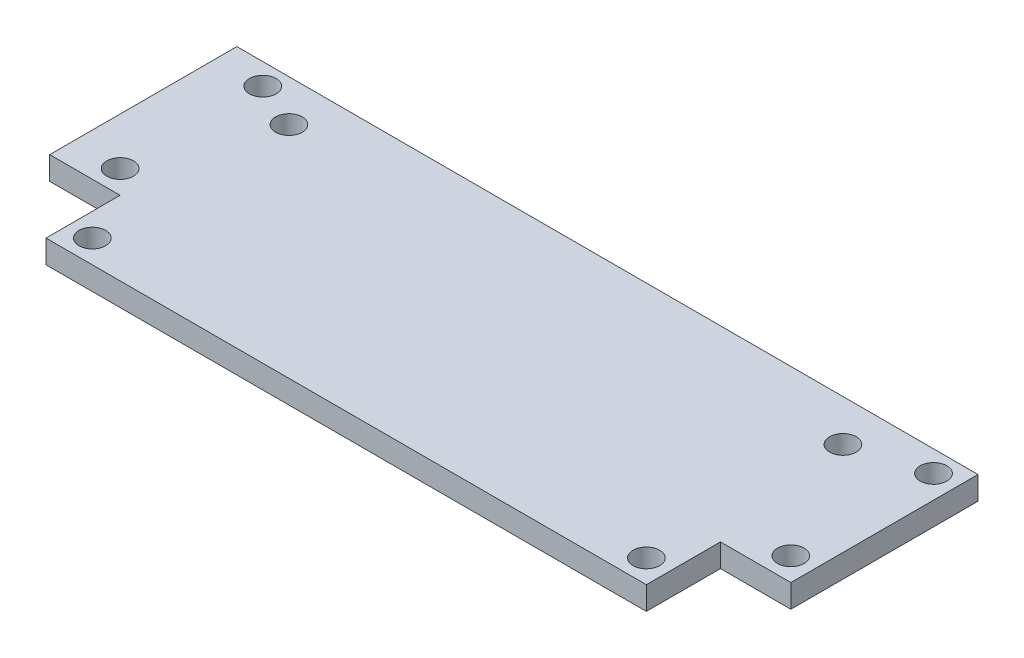
SolidWorks part; units mm, degrees
ref_plane "Front" through (0, 0, 0) normal (0, 0, 1) x (1, 0, 0)
ref_plane "Top" through (0, 0, 0) normal (0, 1, 0) x (1, 0, 0)
ref_plane "Right" through (0, 0, 0) normal (1, 0, 0) x (0, 0, -1)
sketch "Sketch2" plane through (0, 0, 0) normal (0, 1, 0) x (1, 0, 0)
  line L1 (50.8, -17.907) -> (-50.8, -17.907)
  line L2 (50.8, -17.907) -> (50.8, 17.907)
  line L3 (50.8, 17.907) -> (-50.8, 17.907)
  line L4 (-50.8, -17.907) -> (-50.8, 17.907)
  line L5 (50.8, -17.907) -> (-50.8, 17.907) construction
  line L6 (50.8, 17.907) -> (-50.8, -17.907) construction
  point P0 (0, 0)
  dimension "D1" = 101.6
  dimension "D2" = 35.814
extrude "Boss-Extrude1" add sketch "Sketch2" along normal blind 3.175
sketch "Sketch3" plane through (0, 3.175, 0) normal (0, 1, 0) x (1, 0, 0)
  line L0 (50.8, 17.907) -> (47.625, 17.907) construction
  line L1 (50.8, 17.907) -> (-50.8, 17.907) construction
  line L2 (47.625, 17.907) -> (47.625, 14.986) construction
  line L3 (47.625, 14.986) -> (47.625, -4.572) construction
  line L4 (-50.8, 17.907) -> (-47.498, 17.907) construction
  line L5 (-47.498, 17.907) -> (-47.498, -17.907) construction
  line L6 (-50.8, -17.907) -> (50.8, -17.907) construction
  line L7 (-47.498, 17.907) -> (-44.323, 17.907) construction
  line L8 (-44.323, 17.907) -> (-44.323, 14.986) construction
  line L9 (-44.323, 14.986) -> (-44.323, -4.572) construction
  circle A0 centre (47.625, 14.986) radius 1.8288
  circle A1 centre (47.625, -4.572) radius 1.8288
  circle A2 centre (-44.323, 14.986) radius 1.8288
  circle A3 centre (-44.323, -4.572) radius 1.8288
  dimension "D3" = 3.6576
  dimension "D5" = 3.6576
  dimension "D9" = 3.6576
  dimension "D10" = 3.6576
  dimension "D1" = 3.175
  dimension "D2" = 2.921
  dimension "D4" = 19.558
  dimension "D6" = 3.302
  dimension "D7" = 3.175
  dimension "D8" = 2.921
extrude "Cut-Extrude1" cut sketch "Sketch3" against normal through all
sketch "Sketch4" plane through (0, 3.175, 0) normal (0, 1, 0) x (1, 0, 0)
  line L0 (0, 17.907) -> (0, -17.907) construction
  line L1 (50.8, 17.907) -> (-50.8, 17.907) construction
  line L2 (-50.8, -17.907) -> (50.8, -17.907) construction
  line L3 (-44.323, 14.986) -> (-37.973, 14.986) construction
  line L4 (-37.973, -17.907) -> (-37.973, -14.732) construction
  line L5 (-37.973, -14.732) -> (-37.973, 12.2174) construction
  circle A0 centre (-37.973, -14.732) radius 1.8288
  circle A1 centre (-37.973, 12.2174) radius 1.8288
  circle A2 centre (37.973, -14.732) radius 1.8288
  circle A3 centre (37.973, 12.2174) radius 1.8288
  dimension "D2" = 3.175
  dimension "D4" = 26.9494
  dimension "D3" = 3.6576
  dimension "D1" = 6.35
extrude "Cut-Extrude2" cut sketch "Sketch4" against normal through all
sketch "Sketch5" plane through (0, 3.175, 0) normal (0, 1, 0) x (1, 0, 0)
  line L0 (37.973, -14.732) -> (41.148, -14.732) construction
  line L1 (47.625, -4.572) -> (47.625, -7.747) construction
  line L2 (50.8, -17.907) -> (50.8, -7.747)
  line L3 (50.8, -17.907) -> (41.1484, -17.907)
  line L4 (50.8, -7.747) -> (41.1484, -7.747)
  line L5 (41.1484, -17.907) -> (41.1484, -7.747)
  line L6 (50.8, -17.907) -> (50.8, 17.907) construction
  line L7 (0, -17.907) -> (0, 17.907) construction
  line L8 (-50.8, -17.907) -> (50.8, -17.907) construction
  line L9 (50.8, 17.907) -> (-50.8, 17.907) construction
  line L10 (-50.8, -17.907) -> (-50.8, -7.747)
  line L11 (-50.8, -17.907) -> (-41.1484, -17.907)
  line L12 (-41.1484, -17.907) -> (-41.1484, -7.747)
  line L13 (-50.8, -7.747) -> (-41.1484, -7.747)
  dimension "D1" = 3.175
  dimension "D2" = 3.175
extrude "Cut-Extrude3" cut sketch "Sketch5" against normal through all
